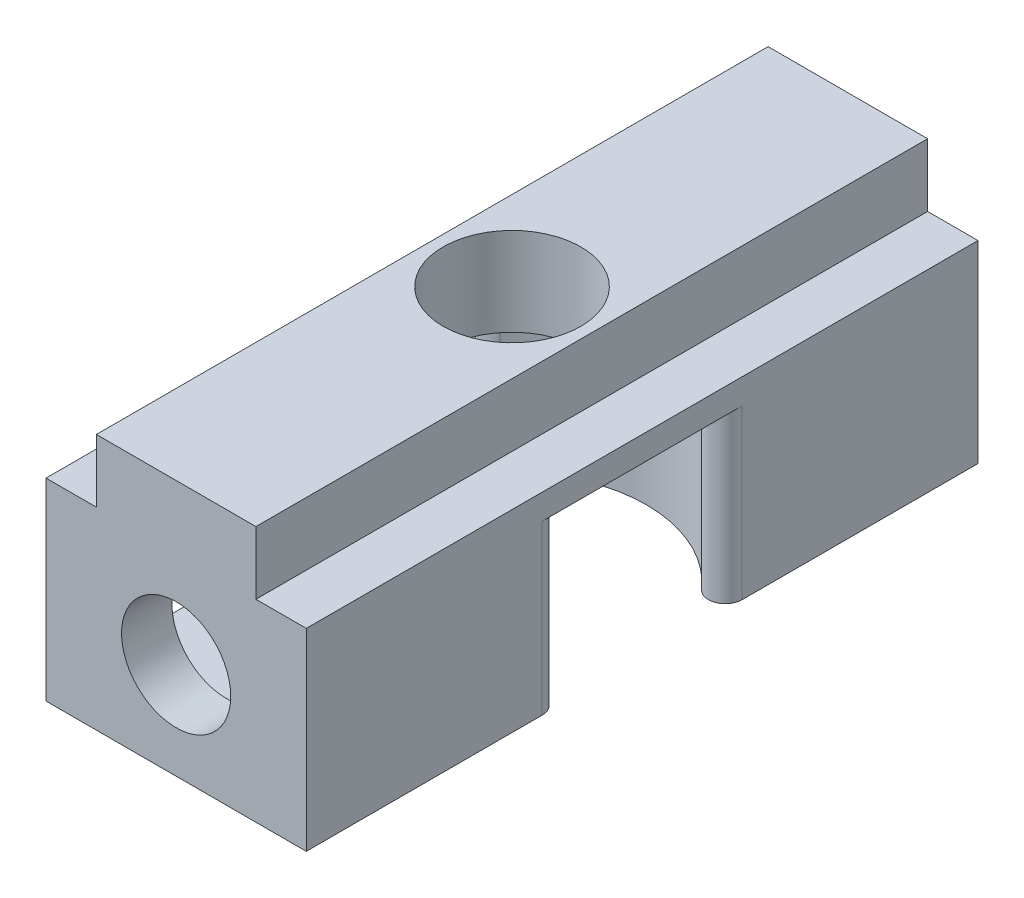
SolidWorks part; units mm, degrees
ref_plane "Front Plane" through (0, 0, 0) normal (1, 0, 0) x (0, 1, 0)
ref_plane "Top Plane" through (0, 0, 0) normal (0, 0, 1) x (0, 1, 0)
ref_plane "Right Plane" through (0, 0, 0) normal (0, 1, 0) x (-1, 0, 0)
sketch "Sketch1" plane through (0, 0, 0) normal (0, 0, 1) x (0, 1, 0)
  line L0 (0, 0) -> (0, 15.5)
  line L1 (0, 15.5) -> (11.5, 15.5)
  line L2 (11.5, 15.5) -> (11.5, 12.5)
  line L3 (11.5, 12.5) -> (15.25, 12.5)
  line L4 (15.25, 12.5) -> (15.25, 3)
  line L5 (15.25, 3) -> (11.5, 3)
  line L6 (11.5, 3) -> (11.5, 0)
  line L7 (11.5, 0) -> (0, 0)
  dimension "D1" = 3.75
  dimension "D2" = 15.5
  dimension "D3" = 9.5
  dimension "D4" = 11.5
extrude "Boss-Extrude1" add sketch "Sketch1" along normal blind 40
sketch "Sketch2" plane through (0, 15.25, 0) normal (0, 1, 0) x (-1, 0, 0)
  line L0 (0, 40) -> (15.5, 0) construction
  circle A0 centre (7.75, 20) radius 4.1
  dimension "D1" = 8.2
extrude "Cut-Extrude1" cut sketch "Sketch2" against normal up to next
sketch "Sketch3" plane through (0, 0, 0) normal (0, -1, 0) x (1, 0, 0)
  circle A0 centre (-7.75, 20) radius 8
  dimension "D1" = 16
extrude "Cut-Extrude2" cut sketch "Sketch3" against normal blind 10
fillet "Fillet1" radius 1 4 edges at (0, 5, 18.0157) (0, 5, 21.9843) (-15.5, 5, 21.9843) (-15.5, 5, 18.0157)
sketch "Sketch4" plane through (0, 0, 40) normal (0, 0, 1) x (1, 0, 0)
  line L0 (-15.5, 11.5) -> (0, 0) construction
  circle A0 centre (-7.75, 5.75) radius 3.25
  dimension "D1" = 6.5
ref_plane "Plane1" through (0, 0, 37) normal (0, 0, 1) x (1, 0, 0)
sketch "Sketch5" plane through (0, 0, 37) normal (0, 0, 1) x (1, 0, 0)
  line L1 (-1.9765, 5.75) -> (-4.8632, 10.75)
  line L2 (-4.8632, 10.75) -> (-10.6368, 10.75)
  line L3 (-10.6368, 10.75) -> (-13.5235, 5.75)
  line L4 (-13.5235, 5.75) -> (-10.6368, 0.75)
  line L5 (-10.6368, 0.75) -> (-4.8632, 0.75)
  line L6 (-4.8632, 0.75) -> (-1.9765, 5.75)
  circle A0 centre (-7.75, 5.75) radius 5 construction
  dimension "D1" = 10
extrude "Cut-Extrude3" cut sketch "Sketch5" against normal blind 6
sketch "Sketch6" plane through (-15.5, 0, 0) normal (-1, 0, 0) x (0, -1, 0)
  line L0 (-10.75, 37) -> (-5.75, 37) construction
  line L1 (-10.75, 37) -> (-0.75, 37)
  line L2 (-10.75, 37) -> (-10.75, 31)
  line L3 (-10.75, 31) -> (-0.75, 31)
  line L4 (-0.75, 37) -> (-0.75, 31)
  line L5 (-5.75, 37) -> (-10.75, 37) construction
  dimension "D1" = 6
extrude "Cut-Extrude4" cut sketch "Sketch6" against normal up to next
extrude "Cut-Extrude5" cut sketch "Sketch4" against normal blind 3
